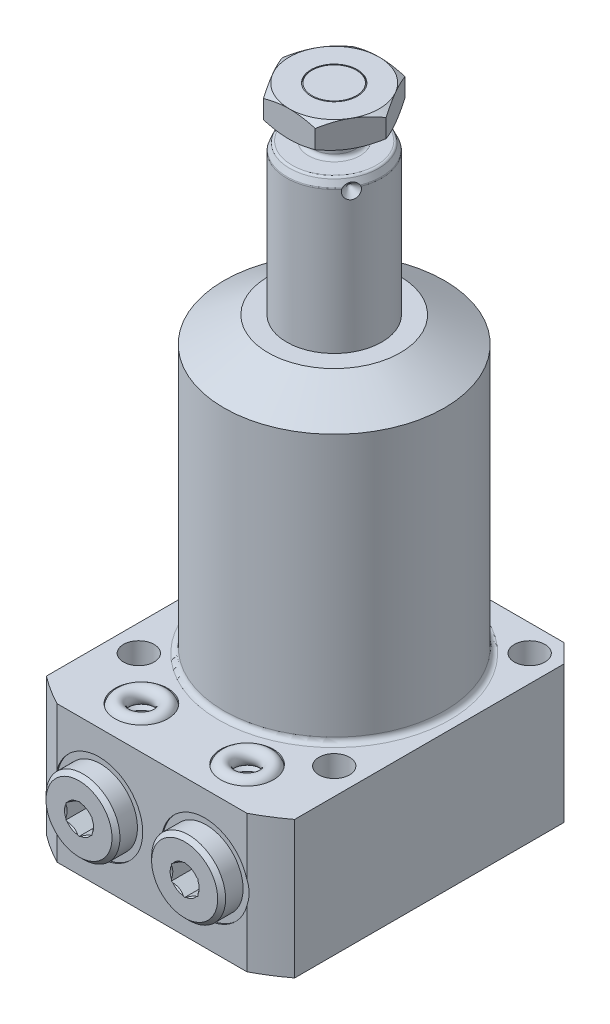
SolidWorks part; units mm, degrees
material "AISI 1020"
ref_plane "Front Plane" through (0, 0, 0) normal (0, 0, 1) x (1, 0, 0)
ref_plane "Top Plane" through (0, 0, 0) normal (0, 1, 0) x (1, 0, 0)
ref_plane "Right Plane" through (0, 0, 0) normal (1, 0, 0) x (0, 0, -1)
sketch "Sketch1" plane through (0, 0, 0) normal (0, 0, 1) x (1, 0, 0)
  line L0 (9, 0) -> (9, 82.5)
  line L1 (9, 82.5) -> (8.3005, 84)
  line L2 (8.3005, 84) -> (4.125, 84)
  line L3 (4.125, 84) -> (4.125, 86)
  line L4 (4.125, 86) -> (4.935, 86.81)
  line L5 (4.935, 86.81) -> (4.935, 92.75)
  line L6 (4.935, 92.75) -> (4.185, 93.5)
  line L7 (4.185, 93.5) -> (0, 93.5)
  line L8 (0, -3.075) -> (0, 64.575) construction
  line L9 (9, 0) -> (0, 0)
  line L10 (0, 0) -> (0, 93.5)
  line L11 (-8.7831, -26) -> (23.6281, -26) construction
  dimension "D1" = 9.5
  dimension "D2" = 18
  dimension "D3" = 8.25
  dimension "D4" = 9.87
  dimension "D5" = 119.5
  dimension "D6" = 25
  dimension "D7" = 1.5
  dimension "D8" = 45
  dimension "D9" = 0.75
  dimension "D10" = 6.69
  dimension "D11" = 4.185
  dimension "D12" = 26
revolve "Revolve2" add sketch "Sketch1" angle 360 about L8
fillet "Fillet2" radius 0.75 2 edges at (0, 84, -4.125) (0, 86, -4.125)
fillet "Fillet3" radius 0.5 2 edges at (0, 82.5, -9) (0, 84, -8.3005)
sketch "Sketch2" plane through (0, 0, 0) normal (1, 0, 0) x (0, 0, -1)
  line L0 (7.5, 82) -> (9, 80.5)
  line L1 (4.2016, 82) -> (7.575, 82) construction
  line L2 (7.982, 84) -> (-7.982, 84) construction
  line L3 (9, 80.5) -> (9, 82)
  line L4 (9, 82) -> (7.5, 82)
  line L5 (9, 0) -> (9, 82.3892) construction
  dimension "D1" = 2
  dimension "D2" = 45
  dimension "D3" = 3
revolve "Cut-Revolve1" cut sketch "Sketch2" angle 360 about L1
sketch "Sketch3" plane through (0, 93.5, 0) normal (0, 1, 0) x (1, 0, 0)
  line L1 (9.815, 0) -> (4.9075, 8.5)
  line L2 (4.9075, 8.5) -> (-4.9075, 8.5)
  line L3 (-4.9075, 8.5) -> (-9.815, 0)
  line L4 (-9.815, 0) -> (-4.9075, -8.5)
  line L5 (-4.9075, -8.5) -> (4.9075, -8.5)
  line L6 (4.9075, -8.5) -> (9.815, 0)
  circle A0 centre (0, 0) radius 8.5 construction
  circle A1 centre (0, 0) radius 4.375
  dimension "D2" = 8.75
  dimension "D1" = 17
extrude "Extrude3" add sketch "Sketch3" against normal blind 5
pattern_circular "CirPattern1" count 3 over 360 about axis through (0, -3.075, 0) along (0, -1, 0) of "Cut-Revolve1"
sketch "Sketch4" plane through (0, 0, 0) normal (1, 0, 0) x (0, 0, -1)
  line L0 (8.5, 93.5) -> (11.5, 93.5)
  line L1 (11.5, 93.5) -> (11.5, 91.7679)
  line L2 (11.5, 91.7679) -> (8.5, 93.5)
  line L3 (8.5, 91) -> (-10.9636, 91) construction
  line L4 (8.5, 88.5) -> (8.5, 93.5) construction
  line L5 (11.5, 90.2321) -> (8.5, 88.5)
  line L6 (11.5, 88.5) -> (11.5, 90.2321)
  line L7 (8.5, 88.5) -> (11.5, 88.5)
  dimension "D1" = 30
  dimension "D2" = 3
revolve "Cut-Revolve3" cut sketch "Sketch4" angle 360 about axis through (0, -3.075, 0) along (0, -1, 0)
sketch "Sketch6" plane through (0, 0, 0) normal (0, 0, 1) x (1, 0, 0)
  line L0 (0, 0) -> (0, 71.3762) construction
  line L1 (0, 55.5) -> (12.5, 55.5)
  line L2 (12.5, 55.5) -> (20.885, 50.6589)
  line L3 (38.895, 0) -> (38.895, -26)
  line L4 (38.895, 0) -> (20.885, 0)
  line L5 (20.885, 50.6589) -> (20.885, 0)
  line L6 (38.895, -26) -> (0, -26)
  line L7 (0, -26) -> (0, 55.5)
  dimension "D1" = 41.77
  dimension "D2" = 26
  dimension "D3" = 81.5
  dimension "D4" = 77.79
  dimension "D5" = 30
  dimension "D6" = 25
revolve "Revolve3" add sketch "Sketch6" angle 360 about L0
sketch "Sketch7" plane through (0, 0, 0) normal (0, 1, 0) x (-1, 0, 0)
  line L0 (0, 0) -> (0, -52.3237) construction
  line L1 (-23.5, 34.5) -> (23.5, 34.5)
  line L2 (-23.5, 34.5) -> (-23.5, -23.5)
  line L3 (-23.5, -23.5) -> (23.5, -23.5)
  line L4 (23.5, 34.5) -> (23.5, -23.5)
  dimension "D1" = 47
  dimension "D2" = 58
  dimension "D3" = 23.5
extrude "Cut-Extrude5" cut sketch "Sketch7" against normal through all flip side to cut
sketch "Sketch8" plane through (0, 0, 0) normal (0, 1, 0) x (-1, 0, 0)
  circle A0 centre (-18.5, 18.5) radius 2.9
  dimension "D1" = 5.8
  dimension "D2" = 18.5
  dimension "D3" = 18.5
extrude "Cut-Extrude6" cut sketch "Sketch8" against normal through all
pattern_circular "CirPattern2" count 4 over 360 about axis through (0, 0, 0) along (0, 1, 0) of "Cut-Extrude6"
chamfer "Chamfer1" distance 3.5 angle 45 2 edges at (-23.5, -13, -23.5) (23.5, -13, -23.5)
fillet "Fillet5" radius 1 1 edges at (0, 0, -20.885)
ref_plane "Plane1" through (0, -13, 0) normal (0, -1, 0) x (1, 0, 0)
sketch "Sketch11" plane through (0, -13, 0) normal (0, -1, 0) x (1, 0, 0)
  line L0 (-10, 42.9716) -> (-10, 19.7499) construction
  line L1 (-18.25, 34.5) -> (-18.25, 34.25)
  line L3 (-18.25, 34.25) -> (-15, 34.25)
  line L4 (-15, 34.25) -> (-14.42, 33.67)
  line L5 (-14.42, 33.67) -> (-14.42, 19.09)
  line L6 (-14.42, 19.09) -> (-10, 19.09)
  line L7 (-10, 19.09) -> (-10, 34.5)
  line L8 (-10, 34.5) -> (-18.25, 34.5)
  line L9 (17.9603, 34.5) -> (-17.9603, 34.5) construction
  dimension "D1" = 10
  dimension "D2" = 0.25
  dimension "D3" = 8.84
  dimension "D4" = 15.16
  dimension "D5" = 16.5
  dimension "D6" = 45
  dimension "D7" = 0.58
revolve "Cut-Revolve5" cut sketch "Sketch11" angle 360 about L0
ref_plane "Plane2" through (0, 0, 26.5) normal (0, 0, 1) x (1, 0, 0)
sketch "Sketch13" plane through (0, 0, 26.5) normal (0, 0, 1) x (1, 0, 0)
  line L0 (-12.5, -14) -> (-12.5, -23.125)
  line L1 (-12.5, -23.125) -> (-13.125, -23.75)
  line L2 (-13.125, -23.75) -> (-15, -23.75)
  line L3 (-15, -23.75) -> (-15, -26)
  line L5 (-15, -26) -> (-10, -26)
  line L6 (-10, -26) -> (-10, -14)
  line L7 (-10, -14) -> (-12.5, -14)
  line L8 (-10, 15.2099) -> (-10, -4.3918) construction
  line L9 (17.9603, -26) -> (-17.9603, -26) construction
  dimension "D1" = 10
  dimension "D2" = 5
  dimension "D3" = 12
  dimension "D4" = 2.25
  dimension "D5" = 10
  dimension "D6" = 45
  dimension "D7" = 0.625
revolve "Cut-Revolve6" cut sketch "Sketch13" angle 360 about L8
mirror "Mirror4" about plane through (0, -13, 0) normal (0, -1, 0) of "Cut-Revolve6"
sketch "Sketch14" plane through (0, -13, 0) normal (0, -1, 0) x (1, 0, 0)
  line L0 (-10, 32.5881) -> (-10, 43.3353) construction
  line L1 (-10, 19.09) -> (-10, 33.67) construction
  line L2 (-12.75, 38.31) -> (-16.25, 38.31)
  line L3 (-16.25, 38.31) -> (-17, 37.56)
  line L4 (-17, 37.56) -> (-17, 34.25)
  line L5 (-1.75, 34.25) -> (-18.25, 34.25) construction
  line L6 (-17, 34.25) -> (-14.125, 34.25)
  line L7 (-5, 34.25) -> (-15, 34.25) construction
  line L8 (-14.125, 34.25) -> (-14.125, 31.8078)
  line L9 (-14.125, 31.8078) -> (-10, 31.8078)
  line L10 (-10, 31.8078) -> (-10, 31.8088)
  line L11 (-10, 31.8088) -> (-12.5, 33.311)
  line L12 (-12.5, 33.311) -> (-12.5, 38.06)
  line L13 (-12.5, 38.06) -> (-12.75, 38.31)
  dimension "D1" = 8.25
  dimension "D2" = 2.4422
  dimension "D3" = 59
  dimension "D4" = 5
  dimension "D5" = 4.06
  dimension "D6" = 14
  dimension "D7" = 45
  dimension "D8" = 0.75
  dimension "D9" = 45
  dimension "D10" = 0.25
  dimension "D11" = 0.001
revolve "Revolve6" add sketch "Sketch14" angle 360 about L0
sketch "Sketch15" plane through (0, 0, 38.31) normal (0, 0, 1) x (1, 0, 0)
  line L1 (-7.5, -14.4434) -> (-7.5, -11.5566)
  line L2 (-7.5, -11.5566) -> (-10, -10.1132)
  line L3 (-10, -10.1132) -> (-12.5, -11.5566)
  line L4 (-12.5, -11.5566) -> (-12.5, -14.4434)
  line L5 (-12.5, -14.4434) -> (-10, -15.8868)
  line L6 (-10, -15.8868) -> (-7.5, -14.4434)
  circle A0 centre (-10, -13) radius 2.5 construction
  dimension "D1" = 5
extrude "Cut-Extrude8" cut sketch "Sketch15" against normal blind 4.06
mirror "Mirror1" about plane through (0, 0, 0) normal (1, 0, 0) of "Mirror4", "Cut-Revolve5", "Cut-Revolve6", "Revolve6", "Cut-Extrude8"
sketch "Sketch16" plane through (0, 0, 26.5) normal (0, 0, 1) x (1, 0, 0)
  line L1 (-10, 9.3219) -> (-10, -15.1063) construction
  line L2 (-10, -23.125) -> (-10, -16.6451) construction
  line L4 (17.9603, -26) -> (-17.9603, -26) construction
  circle A0 centre (-13.5, -25.25) radius 1.5
  dimension "D1" = 3
  dimension "D3" = 0.75
  dimension "D2" = 7
revolve "Revolve7" add sketch "Sketch16" angle 360 about L1
mirror "Mirror3" about plane through (0, 0, 0) normal (1, 0, 0) of bodies 128
mirror "Mirror5" about plane through (0, -13, 0) normal (0, -1, 0) of bodies 128 130
